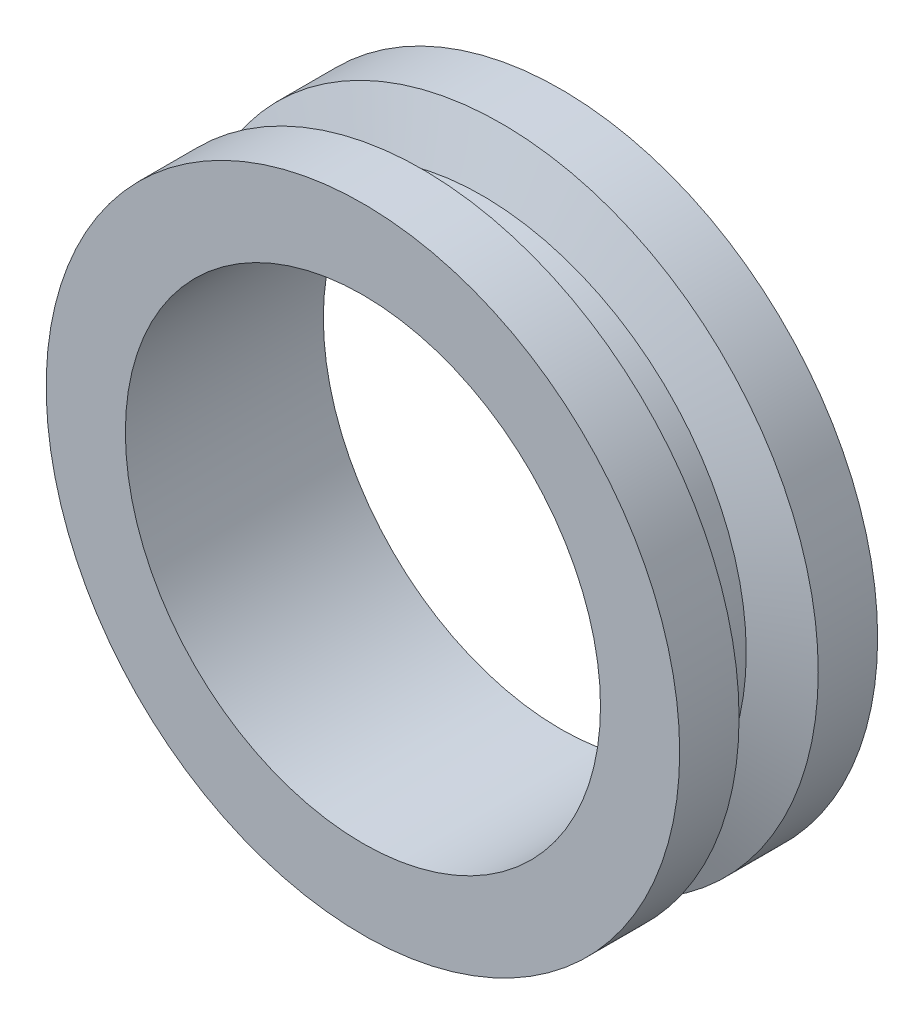
SolidWorks part; units mm, degrees
material "Nailon 101"
ref_plane "Alzado" through (0, 0, 0) normal (0, 0, 1) x (1, 0, 0)
ref_plane "Planta" through (0, 0, 0) normal (0, 1, 0) x (1, 0, 0)
ref_plane "Vista lateral" through (0, 0, 0) normal (1, 0, 0) x (0, 0, -1)
sketch "Croquis1" plane through (0, 0, 0) normal (0, 1, 0) x (1, 0, 0)
  line L0 (0, 0) -> (18, 0) construction
  line L1 (0, -7.5) -> (0, 7.5) construction
  line L2 (0, 7.5) -> (18, 7.5) construction
  line L3 (18, 7.5) -> (18, -7.5)
  line L4 (18, -7.5) -> (0, -7.5) construction
  line L5 (18, 7.5) -> (24, 7.5)
  line L6 (24, 7.5) -> (24, 3)
  line L7 (24, 3) -> (20, 1.5441)
  line L8 (20, 1.5441) -> (20, -1.5441)
  line L9 (20, -1.5441) -> (24, -3)
  line L10 (24, -3) -> (24, -7.5)
  line L11 (24, -7.5) -> (18, -7.5)
  line L12 (18, 0) -> (20, 0) construction
  dimension "D1" = 4
  dimension "D2" = 40
  dimension "D3" = 6
  dimension "D4" = 18
  dimension "D5" = 6
  dimension "D6" = 15
revolve "Revolución1" add sketch "Croquis1" angle 360 about L1
